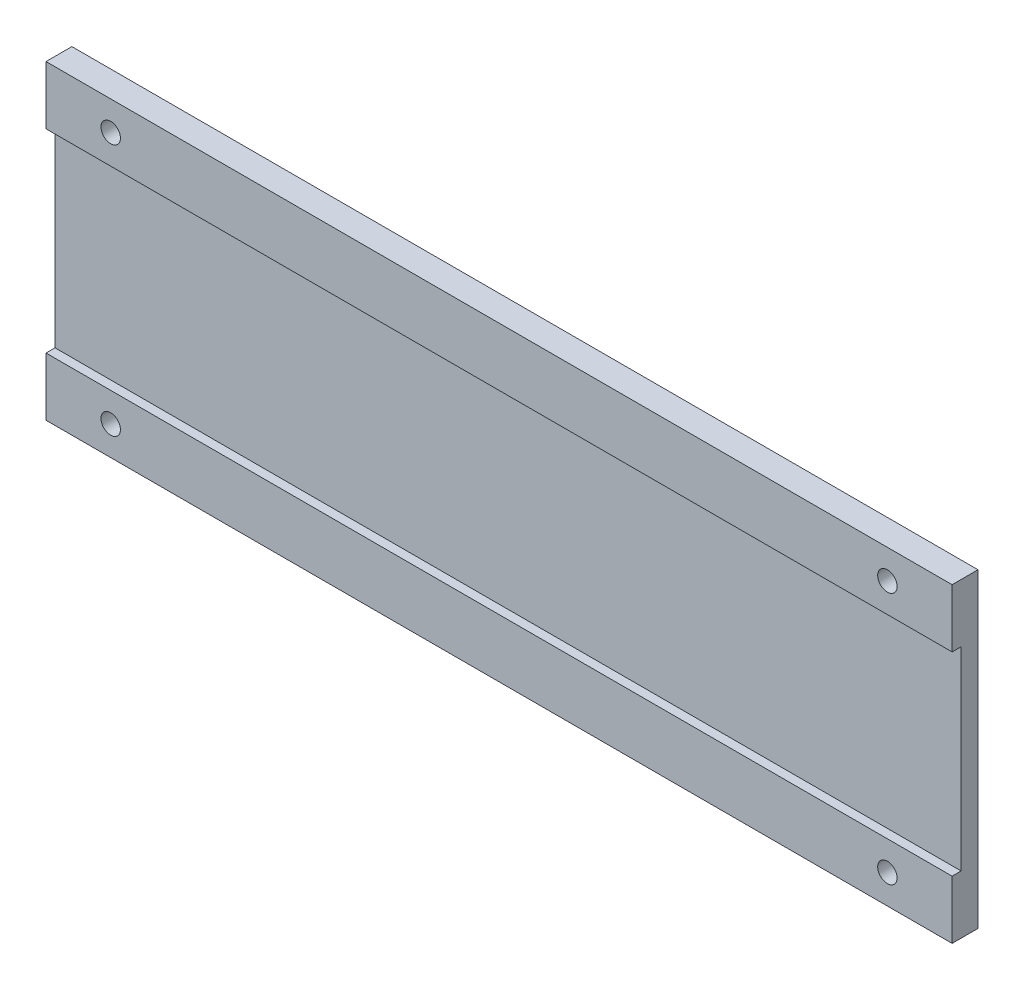
SolidWorks part; units mm, degrees
ref_plane "Plan de face" through (0, 0, 0) normal (0, 0, 1) x (1, 0, 0)
ref_plane "Plan de dessus" through (0, 0, 0) normal (0, 1, 0) x (1, 0, 0)
ref_plane "Plan de droite" through (0, 0, 0) normal (1, 0, 0) x (0, 0, -1)
sketch "Esquisse1" plane through (0, 0, 0) normal (0, 0, 1) x (1, 0, 0)
  line L1 (-33.559, 25.9394) -> (106.441, 25.9394)
  line L2 (-33.559, 25.9394) -> (-33.559, -22.0606)
  line L3 (-33.559, -22.0606) -> (106.441, -22.0606)
  line L4 (106.441, 25.9394) -> (106.441, -22.0606)
  dimension "D1" = 48
  dimension "D2" = 140
extrude "Boss.-Extru.1" add sketch "Esquisse1" along normal blind 4
sketch "Esquisse2" plane through (-33.559, 0, 0) normal (-1, 0, 0) x (0, 0, 1)
  line L0 (4, 25.9394) -> (4, -22.0606) construction
  line L1 (4, 16.9394) -> (2.6099, 16.9394)
  line L2 (4, 16.9394) -> (4, -13.0606)
  line L3 (4, -13.0606) -> (2.6099, -13.0606)
  line L4 (2.6099, 16.9394) -> (2.6099, -13.0606)
  line L5 (4, 25.9394) -> (0, 25.9394) construction
  line L6 (4, -22.0606) -> (0, -22.0606) construction
  dimension "D1" = 9
  dimension "D2" = 9
extrude "Enlèv. mat.-Extru.1" cut sketch "Esquisse2" against normal through all
sketch "Esquisse4" plane through (0, 0, 4) normal (0, 0, 1) x (1, 0, 0)
  line L0 (106.441, 25.9394) -> (-33.559, 25.9394) construction
  line L1 (-33.559, 25.9394) -> (-33.559, 16.9394) construction
  line L2 (-33.559, -13.0606) -> (-33.559, -22.0606) construction
  line L3 (-33.559, -22.0606) -> (106.441, -22.0606) construction
  line L4 (106.441, 16.9394) -> (106.441, 25.9394) construction
  line L5 (106.441, -22.0606) -> (106.441, -13.0606) construction
  circle A0 centre (-23.559, 21.4394) radius 1.5
  circle A1 centre (96.441, 21.4394) radius 1.5
  circle A2 centre (-23.559, -17.5606) radius 1.5
  circle A3 centre (96.441, -17.5606) radius 1.5
  dimension "D1" = 3
  dimension "D2" = 4.5
  dimension "D3" = 10
  dimension "D4" = 10
  dimension "D5" = 4.5
  dimension "D6" = 3
  dimension "D7" = 3
  dimension "D8" = 3
  dimension "D9" = 4.5
  dimension "D10" = 4.5
  dimension "D11" = 10
  dimension "D12" = 10
  dimension "D13" = 120
extrude "Enlèv. mat.-Extru.3" cut sketch "Esquisse4" against normal blind 6
